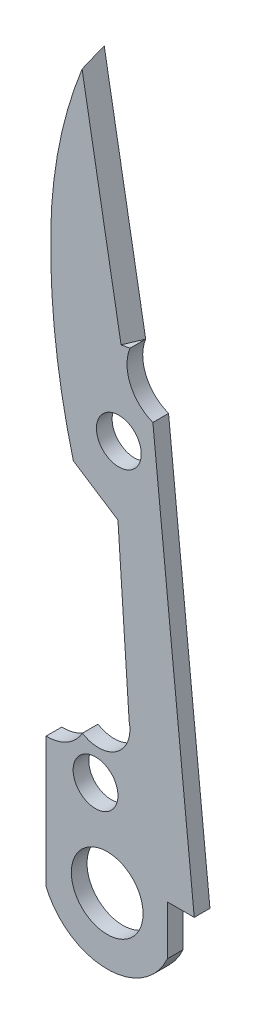
SolidWorks part; units mm, degrees
material "AISI 4340 Steel, normalized"
ref_plane "Front Plane" through (0, 0, 0) normal (0, 0, 1) x (1, 0, 0)
ref_plane "Top Plane" through (0, 0, 0) normal (0, 1, 0) x (1, 0, 0)
ref_plane "Right Plane" through (0, 0, 0) normal (1, 0, 0) x (0, 0, -1)
sketch "Sketch1" plane through (0, 0, 0) normal (0, 0, 1) x (1, 0, 0)
  line L0 (16.7881, 37.7732) -> (83.9405, 37.7732) construction
  line L1 (53.8828, 59.4217) -> (56.23, 46.2137)
  line L2 (57.5259, 43.2165) -> (59.8706, 20.1025)
  line L3 (59.8706, 20.1025) -> (58.3466, 20.1025)
  line L4 (58.3466, 20.1025) -> (58.3466, 17.3085)
  line L5 (51.4751, 24.8023) -> (51.4751, 17.4363)
  line L6 (53.0196, 39.0848) -> (55.5476, 37.4338)
  line L7 (55.5476, 37.4338) -> (56.1826, 27.8834)
  arc A0 (51.7414, 49.7491) -> (53.0196, 39.0848) centre (91.1076, 49.0585) ccw
  arc A1 (51.7414, 49.7491) -> (53.8828, 59.4217) centre (76.6296, 49.3125) cw
  arc A2 (56.23, 46.2137) -> (57.5259, 43.2165) centre (58.3466, 45.3501) ccw
  arc A3 (51.4751, 17.4363) -> (58.3466, 17.3085) centre (54.938, 18.8325) ccw
  arc A4 (56.1826, 27.8834) -> (53.5294, 25.9714) centre (54.4478, 27.4939) cw
  arc A5 (53.5294, 25.9714) -> (51.4751, 24.8023) centre (51.5344, 27.0875) cw
  circle A6 centre (55.5984, 41.3369) radius 1.27
  circle A7 centre (54.2776, 23.9125) radius 1.27
  dimension "D1" = 2.54
  dimension "D3" = 5.08
  dimension "D7" = 3.5814
  dimension "D8" = 2.7432
  dimension "D12" = 2.794
  dimension "D13" = 1.524
  dimension "D29" = 1.27
  dimension "D30" = 1.905
  dimension "D5" = 3.7338
  dimension "D6" = 3.175
  dimension "D14" = 3.81
  dimension "D9" = 0.1702
  dimension "D24" = 35.5092
  dimension "D25" = 13.208
  dimension "D26" = 23.114
  dimension "D27" = 9.5504
  dimension "D4" = 0.6604
  dimension "D10" = 1.778
  dimension "D11" = 2.286
  dimension "D15" = 21.4376
  dimension "D16" = 25.4
  dimension "D17" = 17.4244
  dimension "D18" = 1.3208
  dimension "D19" = 22.352
  dimension "D20" = 2.286
  dimension "D21" = 25.146
  dimension "D22" = 36.83
  dimension "D23" = 24.892
  dimension "D2" = 7.366
  dimension "D28" = 1.651
extrude "Boss-Extrude3" add sketch "Sketch1" along normal blind 0.889
sketch "Sketch3" plane through (0, 0, 0.889) normal (0, 0, 1) x (1, 0, 0)
  circle A0 centre (54.938, 18.8325) radius 2.032
  dimension "D1" = 4.064
extrude "Cut-Extrude1" cut sketch "Sketch3" against normal through all
ref_plane "Plane2" through (-10.5044, 59.1099, 0) normal (-0.175, 0.9846, 0) x (0.9846, 0.175, 0)
sketch "Sketch4" plane through (-10.5044, 59.1099, 0) normal (-0.175, 0.9846, 0) x (0.9846, 0.175, 0)
  line L3 (63.4486, -0.889) -> (63.4486, 0) construction
  line L5 (63.4486, 0) -> (63.4486, -0.889)
  line L6 (63.4486, 0) -> (59.6478, 0) construction
  line L7 (59.6478, -0.889) -> (63.4486, -0.889) construction
  line L8 (62.9353, -0.889) -> (63.4486, -0.889)
  line L9 (62.9353, -0.889) -> (63.4486, 0)
  dimension "D1" = 30
extrude "Cut-Extrude2" cut sketch "Sketch4" against normal up to vertex (24.3737 mm away) up to point (56.23, 46.2137, 0)
